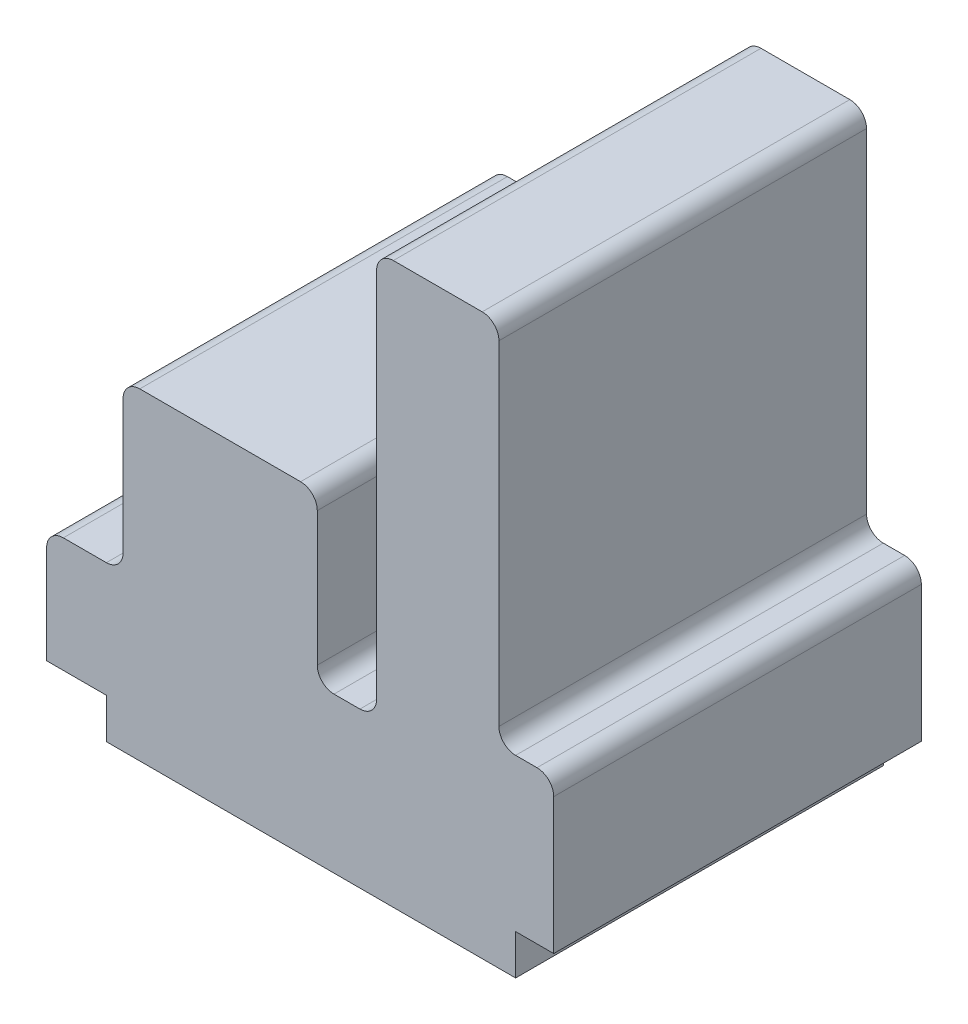
SolidWorks part; units mm, degrees
ref_plane "Ön Düzlem" through (0, 0, 0) normal (0, 0, 1) x (1, 0, 0)
ref_plane "Üst Düzlem" through (0, 0, 0) normal (0, 1, 0) x (1, 0, 0)
ref_plane "Sağ Düzlem" through (0, 0, 0) normal (1, 0, 0) x (0, 0, -1)
sketch "Çizim5" plane through (0, 0, 0) normal (0, 0, 1) x (1, 0, 0)
  line L0 (3, 27.8379) -> (10.7233, 27.8379)
  line L1 (10.7233, 0) -> (84.1934, 0)
  line L2 (0, 7.2203) -> (0, 24.8379)
  line L3 (62.2414, 100.5717) -> (78.1934, 100.5717)
  line L4 (91.0333, 7.2203) -> (91.0333, 31.6172)
  line L5 (13.7233, 30.8379) -> (13.7233, 54.8605)
  line L6 (16.7233, 57.8605) -> (45.5882, 57.8605)
  line L7 (48.5882, 54.8605) -> (48.5882, 30.8379)
  line L8 (51.5882, 27.8379) -> (56.2414, 27.8379)
  line L9 (59.2414, 30.8379) -> (59.2414, 97.5717)
  line L10 (81.1934, 97.5717) -> (81.1934, 37.6172)
  line L11 (84.1934, 34.6172) -> (88.0333, 34.6172)
  line L12 (0, 7.2203) -> (10.7233, 7.2203)
  line L13 (10.7233, 7.2203) -> (10.7233, 0)
  line L14 (91.0333, 7.2203) -> (84.1934, 7.2203)
  line L15 (84.1934, 7.2203) -> (84.1934, 0)
  arc A0 (88.0333, 34.6172) -> (91.0333, 31.6172) centre (88.0333, 31.6172) cw
  arc A1 (81.1934, 37.6172) -> (84.1934, 34.6172) centre (84.1934, 37.6172) ccw
  arc A2 (81.1934, 97.5717) -> (78.1934, 100.5717) centre (78.1934, 97.5717) ccw
  arc A3 (59.2414, 97.5717) -> (62.2414, 100.5717) centre (62.2414, 97.5717) cw
  arc A4 (56.2414, 27.8379) -> (59.2414, 30.8379) centre (56.2414, 30.8379) ccw
  arc A5 (48.5882, 30.8379) -> (51.5882, 27.8379) centre (51.5882, 30.8379) ccw
  arc A6 (45.5882, 57.8605) -> (48.5882, 54.8605) centre (45.5882, 54.8605) cw
  arc A7 (13.7233, 54.8605) -> (16.7233, 57.8605) centre (16.7233, 54.8605) cw
  arc A8 (10.7233, 27.8379) -> (13.7233, 30.8379) centre (10.7233, 30.8379) ccw
  arc A9 (3, 27.8379) -> (0, 24.8379) centre (3, 24.8379) ccw
  dimension "D1" = 3
extrude "Yükseklik-Ekstrüzyon2" add sketch "Çizim5" along normal blind 66
